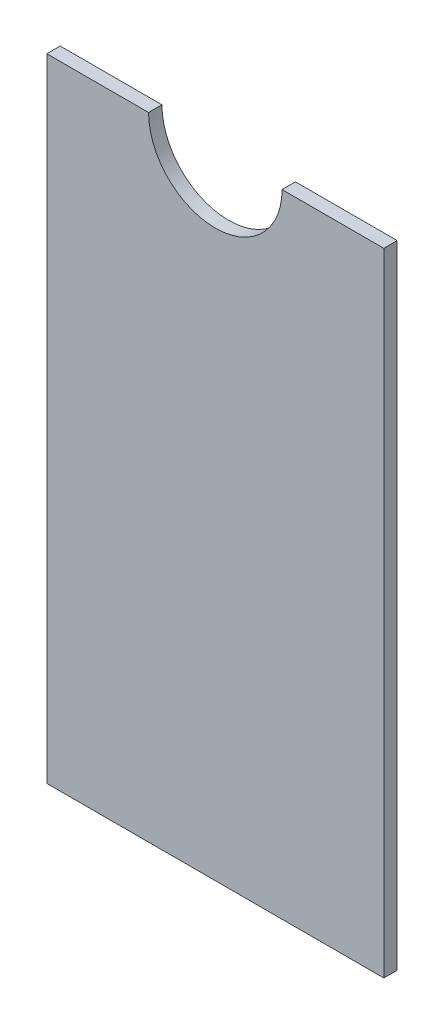
SolidWorks part; units mm, degrees
material "FiberBoard"
ref_plane "Front Plane" through (0, 0, 0) normal (0, 0, 1) x (1, 0, 0)
ref_plane "Top Plane" through (0, 0, 0) normal (0, 1, 0) x (1, 0, 0)
ref_plane "Right Plane" through (0, 0, 0) normal (1, 0, 0) x (0, 0, -1)
sketch "Sketch1" plane through (0, 0, 0) normal (0, 0, 1) x (1, 0, 0)
  line L0 (15.85, 75) -> (40, 75)
  line L1 (-40, 75) -> (-15.85, 75)
  line L2 (-40, 75) -> (-40, -75)
  line L3 (-40, -75) -> (40, -75)
  line L4 (40, 75) -> (40, -75)
  line L5 (-40, 75) -> (40, -75) construction
  line L6 (-40, -75) -> (40, 75) construction
  arc A0 (-15.85, 75) -> (15.85, 75) centre (0, 75) ccw
  point P0 (0, 0)
  point P7 (0, 59.15)
  point P10 (0, -75)
  dimension "D3" = 15.85
  dimension "D1" = 150
  dimension "D2" = 80
extrude "Boss-Extrude1" add sketch "Sketch1" along normal blind 3.175
